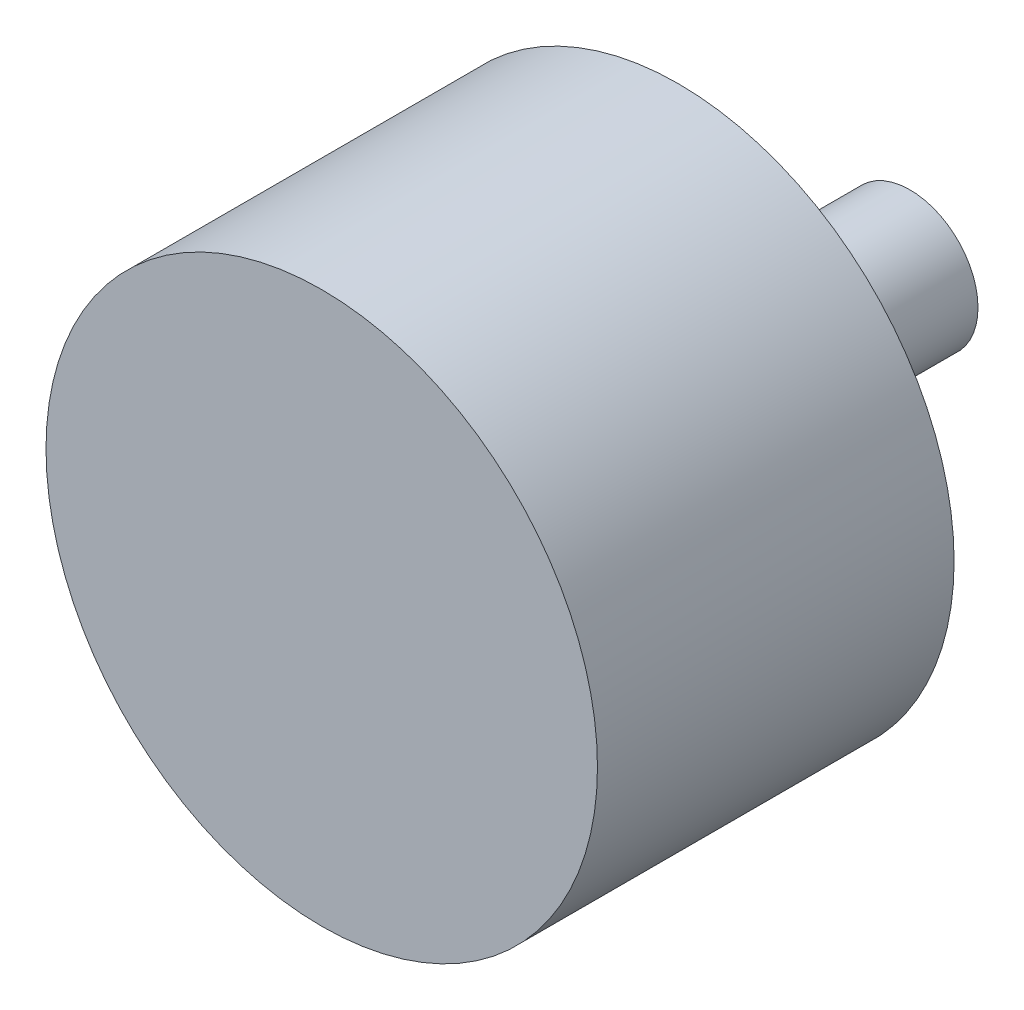
SolidWorks part; units mm, degrees
ref_plane "Front Plane" through (0, 0, 0) normal (0, 0, 1) x (1, 0, 0)
ref_plane "Top Plane" through (0, 0, 0) normal (0, 1, 0) x (1, 0, 0)
ref_plane "Right Plane" through (0, 0, 0) normal (1, 0, 0) x (0, 0, -1)
sketch "Sketch1" plane through (0, 0, 0) normal (1, 0, 0) x (0, 0, -1)
  line L0 (0, 0) -> (53.4361, 0) construction
  line L1 (0, 0) -> (0, 19.05)
  line L2 (0, 19.05) -> (24.638, 19.05)
  line L3 (24.638, 19.05) -> (24.638, 5.461)
  line L4 (24.638, 5.461) -> (30.48, 5.461)
  line L5 (30.48, 5.461) -> (30.48, 4.699)
  line L6 (30.48, 4.699) -> (40.64, 4.699)
  line L7 (40.64, 4.699) -> (40.64, 0)
  line L8 (0, 0) -> (40.64, 0)
  dimension "D1" = 40.64
  dimension "D2" = 38.1
  dimension "D3" = 10.922
  dimension "D4" = 9.398
  dimension "D5" = 5.842
  dimension "D6" = 24.638
revolve "Revolve1" add sketch "Sketch1" angle 360 about L0
